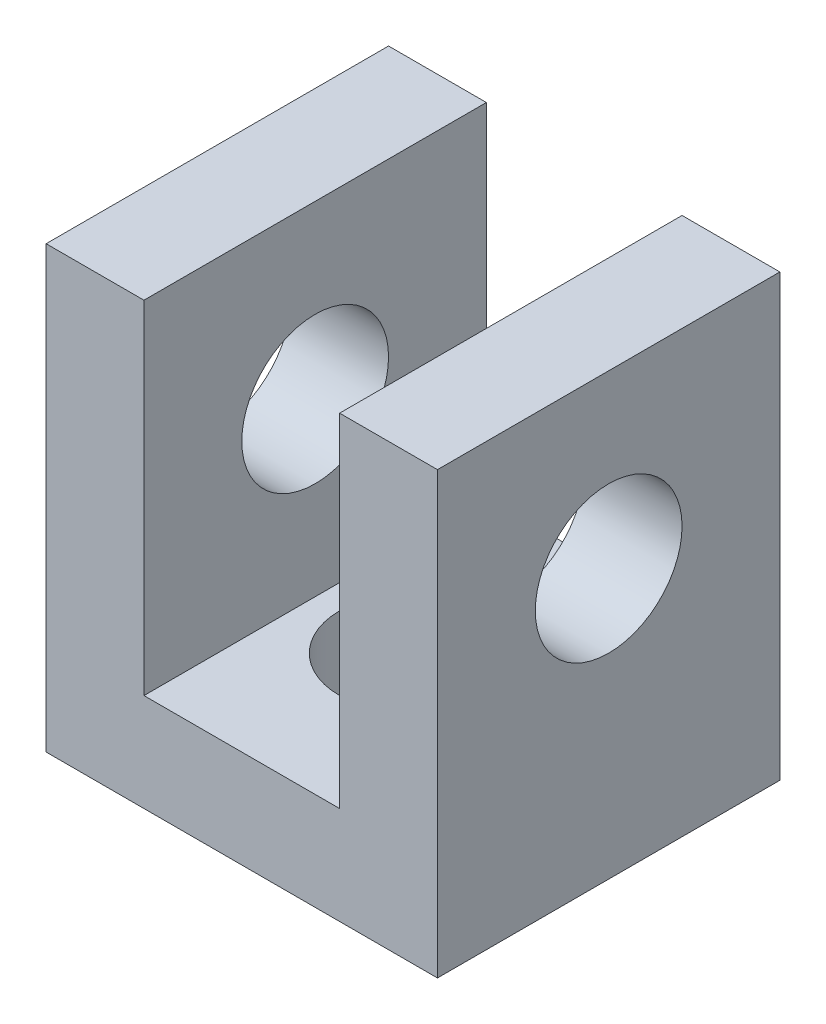
SolidWorks part; units mm, degrees
ref_plane "Front Plane" through (0, 0, 0) normal (0, 0, 1) x (1, 0, 0)
ref_plane "Top Plane" through (0, 0, 0) normal (0, 1, 0) x (1, 0, 0)
ref_plane "Right Plane" through (0, 0, 0) normal (1, 0, 0) x (0, 0, -1)
sketch "Sketch1" plane through (0, 0, 0) normal (0, 0, 1) x (1, 0, 0)
  line L0 (-20, 45) -> (-20, 0)
  line L1 (-20, 0) -> (20, 0)
  line L2 (20, 0) -> (20, 45)
  line L3 (20, 45) -> (10, 45)
  line L4 (10, 45) -> (10, 10)
  line L5 (10, 10) -> (-10, 10)
  line L6 (-10, 10) -> (-10, 45)
  line L7 (-10, 45) -> (-20, 45)
  point P7 (0, 0)
  dimension "D1" = 10
  dimension "D2" = 20
  dimension "D3" = 10
  dimension "D4" = 35
extrude "Boss-Extrude1" add sketch "Sketch1" along normal mid plane 35
sketch "Sketch2" plane through (20, 0, 0) normal (1, 0, 0) x (0, 0, -1)
  line L1 (-17.5, 10) -> (17.5, 10) construction
  line L2 (-17.5, 10) -> (-17.5, 45) construction
  line L3 (-17.5, 45) -> (17.5, 45) construction
  line L4 (17.5, 10) -> (17.5, 45) construction
  line L5 (-17.5, 10) -> (17.5, 45) construction
  line L6 (-17.5, 45) -> (17.5, 10) construction
  circle A0 centre (0, 27.5) radius 7.5
  point P0 (0, 27.5)
  dimension "D2" = 15
  dimension "D1" = 10
extrude "Cut-Extrude1" cut sketch "Sketch2" against normal through all
sketch "Sketch3" plane through (0, 10, 0) normal (0, 1, 0) x (1, 0, 0)
  circle A0 centre (0, 0) radius 7.5
  dimension "D1" = 15
extrude "Cut-Extrude2" cut sketch "Sketch3" against normal through all
